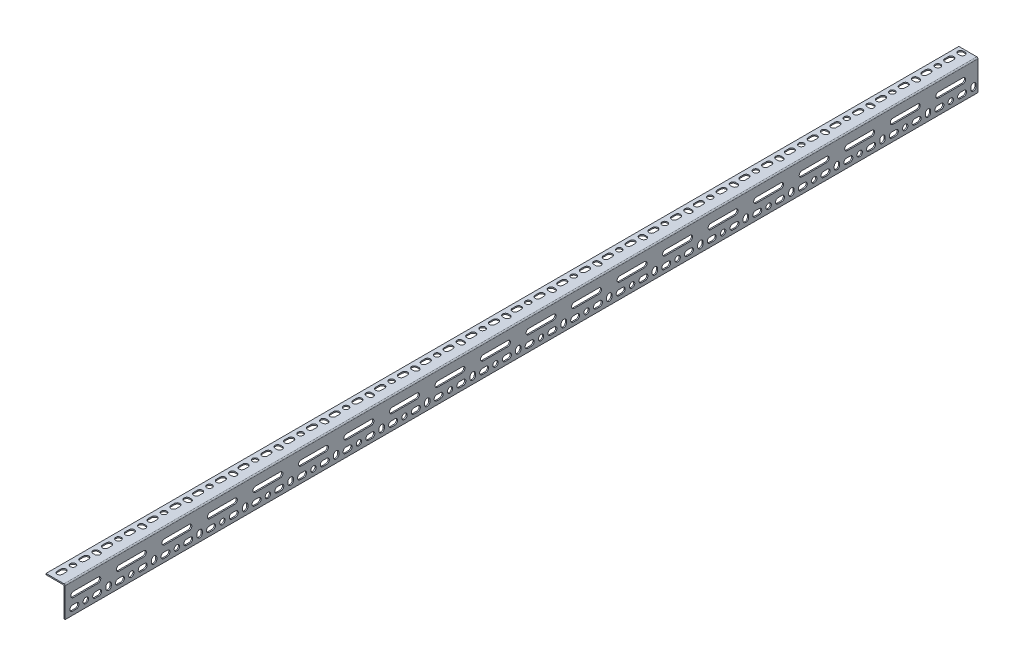
SolidWorks part; units mm, degrees
material "Black Iron Steel"
ref_plane "Front Plane" through (0, 0, 0) normal (0, 0, 1) x (1, 0, 0)
ref_plane "Top Plane" through (0, 0, 0) normal (0, 1, 0) x (1, 0, 0)
ref_plane "Right Plane" through (0, 0, 0) normal (1, 0, 0) x (0, 0, -1)
other "total length"
sketch "Sketch1" plane through (0, 0, 0) normal (0, 1, 0) x (1, 0, 0)
  line L0 (0, 0) -> (0, 1524)
  dimension "D1" = 1524
other "Structural Member1"
ref_plane "Plane1" through (0, 0, 0) normal (0, 0, 1) x (-1, 0, 0)
sketch "Sketch112" plane through (0, 0, 0) normal (0, 0, 1) x (-1, 0, 0)
  line L0 (0, 2) -> (0, 50.8)
  line L1 (0, 50.8) -> (1, 50.8)
  line L2 (2, 49.8) -> (2, 4)
  line L3 (4, 2) -> (31, 2)
  line L4 (32, 1) -> (32, 0)
  line L5 (32, 0) -> (2, 0)
  arc A0 (32, 1) -> (31, 2) centre (31, 1) ccw
  arc A1 (1, 50.8) -> (2, 49.8) centre (1, 49.8) cw
  arc A2 (4, 2) -> (2, 4) centre (4, 4) cw
  arc A3 (0, 2) -> (2, 0) centre (2, 2) ccw
  point P10 (17, 0)
  point P14 (0, 26.4)
  point P15 (2, 26.4)
  point P16 (17, 2)
  point P17 (2, 50.8)
  point P18 (32, 2)
  point P21 (0, 0)
  point P22 (0, 0)
  dimension "Radius_1" = 2
  dimension "D4" = 2
  dimension "D1" = 2
  dimension "H_leg" = 32
  dimension "D2" = 1
  dimension "D3" = 50.8
sketch "Sketch12" plane through (0, 0, 0) normal (0, 1, 0) x (1, 0, 0)
  line L0 (-21.5, 12.5) -> (-21.5, 18.5) construction
  line L1 (-26, 12.5) -> (-26, 18.5)
  line L2 (-17, 12.5) -> (-17, 18.5)
  line L3 (-32, 1524) -> (-32, 0) construction
  line L5 (-2, 0) -> (-32, 0) construction
  arc A0 (-26, 12.5) -> (-17, 12.5) centre (-21.5, 12.5) ccw
  arc A1 (-17, 18.5) -> (-26, 18.5) centre (-21.5, 18.5) ccw
  point P2 (-21.5, 15.5)
  dimension "D1" = 15
  dimension "D4" = 8
  dimension "D2" = 9
  dimension "D3" = 6
extrude "Slot 1.5" cut sketch "Sketch12" against normal through all
sketch "Sketch13" plane through (0, 0, 0) normal (0, 1, 0) x (1, 0, 0)
  line L0 (-21.5, 34.5) -> (-21.5, 15.5) construction
  circle A0 centre (-21.5, 34.5) radius 4.5
  arc A2 (-17, 18.5) -> (-26, 18.5) centre (-21.5, 18.5) ccw construction
  dimension "D1" = 7
  dimension "D2" = 9
extrude "Hole 1.5" cut sketch "Sketch13" against normal through all
sketch "Sketch18" plane through (0, 0, 0) normal (0, 1, 0) x (1, 0, 0)
  line L0 (-21.5, 72.5) -> (-18.5, 72.5) construction
  line L1 (-21.5, 77) -> (-18.5, 77)
  line L2 (-21.5, 68) -> (-18.5, 68)
  arc A0 (-21.5, 77) -> (-21.5, 68) centre (-21.5, 72.5) ccw
  arc A1 (-18.5, 68) -> (-18.5, 77) centre (-18.5, 72.5) ccw
  point P2 (-20, 72.5)
  dimension "D2" = 12
  dimension "D1" = 9
  dimension "D3" = 38
extrude "Vertical Slot 1.5" cut sketch "Sketch18" against normal through all
sketch "Sketch15" plane through (0, 0, 0) normal (1, 0, 0) x (0, 0, -1)
  line L0 (12.5, -40.3) -> (18.5, -40.3) construction
  line L1 (12.5, -35.8) -> (18.5, -35.8)
  line L2 (12.5, -44.8) -> (18.5, -44.8)
  line L6 (0, -50.8) -> (0, -2) construction
  line L7 (1524, -50.8) -> (0, -50.8) construction
  arc A0 (12.5, -35.8) -> (12.5, -44.8) centre (12.5, -40.3) ccw
  arc A1 (18.5, -44.8) -> (18.5, -35.8) centre (18.5, -40.3) ccw
  point P2 (15.5, -40.3)
  dimension "D1" = 15
  dimension "D3" = 8
  dimension "D2" = 9
  dimension "D4" = 6
extrude "Small Slot 2.5" cut sketch "Sketch15" against normal through all
sketch "Sketch16" plane through (0, 0, 0) normal (1, 0, 0) x (0, 0, -1)
  line L0 (34.5, -40.3) -> (15.5, -40.3) construction
  circle A0 centre (34.5, -40.3) radius 4.5
  arc A2 (18.5, -44.8) -> (18.5, -35.8) centre (18.5, -40.3) ccw construction
  dimension "D1" = 9
  dimension "D2" = 7
extrude "Hole 2.5" cut sketch "Sketch16" against normal through all
sketch "Sketch17" plane through (0, 0, 0) normal (1, 0, 0) x (0, 0, -1)
  line L0 (72.5, -37.3) -> (72.5, -40.3) construction
  line L1 (77, -37.3) -> (77, -40.3)
  line L2 (68, -37.3) -> (68, -40.3)
  line L3 (72.5, -40.3) -> (34.5, -40.3) construction
  arc A0 (77, -37.3) -> (68, -37.3) centre (72.5, -37.3) ccw
  arc A1 (68, -40.3) -> (77, -40.3) centre (72.5, -40.3) ccw
  point P2 (72.5, -38.8)
  dimension "D1" = 12
  dimension "D2" = 9
  dimension "D3" = 38
extrude "Vertical Slot 2.5" cut sketch "Sketch17" against normal through all
sketch "Sketch14" plane through (0, 0, 0) normal (1, 0, 0) x (0, 0, -1)
  line L0 (14, -21.25) -> (55, -21.25) construction
  line L1 (14, -16.75) -> (55, -16.75)
  line L2 (14, -25.75) -> (55, -25.75)
  line L8 (34.5, -40.3) -> (34.5, -21.25) construction
  arc A0 (14, -16.75) -> (14, -25.75) centre (14, -21.25) ccw
  arc A1 (55, -25.75) -> (55, -16.75) centre (55, -21.25) ccw
  point P2 (34.5, -21.25)
  dimension "D1" = 50
  dimension "D3" = 19.05
  dimension "D2" = 9
extrude "Long Slot 2.5" cut sketch "Sketch14" against normal through all
pattern_linear "Short Slot pattern 1.5" count 40 spacing 38 along (0, 0, -1) of "Slot 1.5", "Small Slot 2.5"
pattern_linear "Hole pattern" count 20 spacing 76 along (0, 0, -1) of "Hole 2.5", "Hole 1.5"
pattern_linear "Vert Slot Pattern" count 20 spacing 76 along (0, 0, -1) of "Vertical Slot 1.5", "Vertical Slot 2.5"
pattern_linear "Long Slot pattern" count 20 spacing 76 along (0, 0, -1) of "Long Slot 2.5"
equation "\"D4@Sketch112\" = \"Radius_1@Sketch112\""
